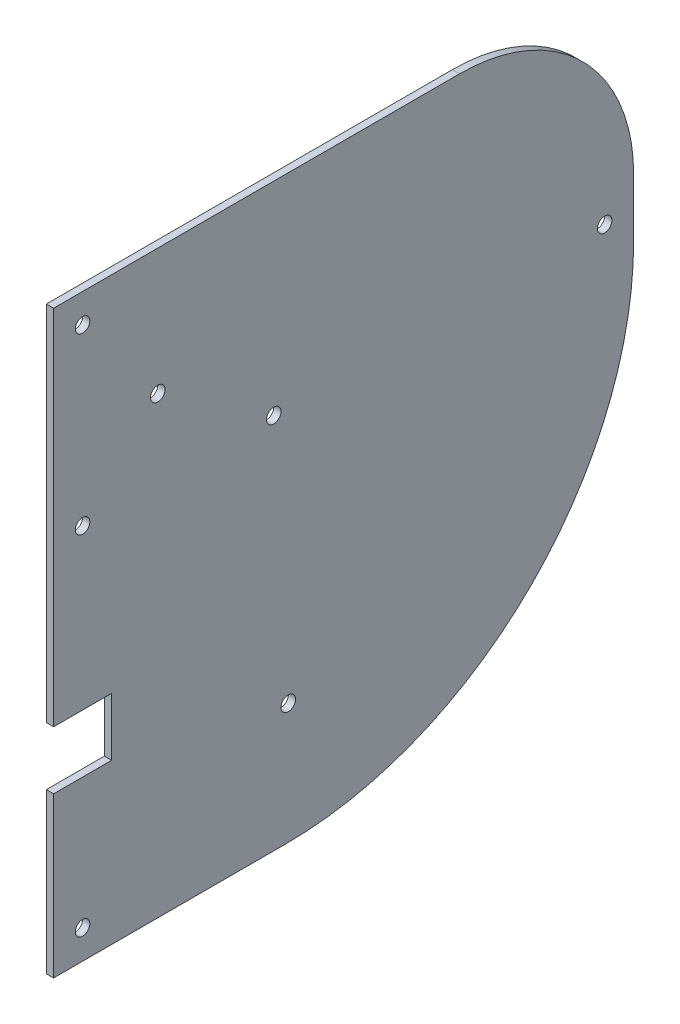
SolidWorks part; units mm, degrees
material "6061-T6 (SS)"
ref_plane "Front Plane" through (0, 0, 0) normal (0, 0, 1) x (1, 0, 0)
ref_plane "Top Plane" through (0, 0, 0) normal (0, 1, 0) x (1, 0, 0)
ref_plane "Right Plane" through (0, 0, 0) normal (1, 0, 0) x (0, 0, -1)
sketch "Sketch1" plane through (0, 0, 0) normal (1, 0, 0) x (0, 0, -1)
  line L1 (0, 0) -> (254, 0)
  line L2 (0, 0) -> (0, 254)
  line L3 (0, 254) -> (254, 254)
  line L4 (254, 0) -> (254, 254)
  line L5 (0, 0) -> (254, 254) construction
  line L6 (0, 254) -> (254, 0) construction
  point P4 (127, 127)
  dimension "D1" = 254
  dimension "D2" = 254
extrude "Boss-Extrude1" add sketch "Sketch1" along normal blind 3.175
sketch "Sketch2" plane through (3.175, 0, 0) normal (1, 0, 0) x (0, 0, -1)
  line L0 (0, 254) -> (0, 0) construction
  line L1 (0, 95.25) -> (25.4, 95.25)
  line L2 (0, 95.25) -> (0, 69.85)
  line L3 (0, 69.85) -> (25.4, 69.85)
  line L4 (25.4, 95.25) -> (25.4, 69.85)
  line L5 (0, 95.25) -> (25.4, 69.85) construction
  line L6 (0, 69.85) -> (25.4, 95.25) construction
  line L7 (0, 0) -> (254, 0) construction
  line L8 (0, 165.1) -> (254, 165.1) construction
  line L9 (254, 0) -> (254, 254) construction
  line L10 (12.7, 254) -> (12.7, 0) construction
  line L11 (254, 254) -> (0, 254) construction
  circle A0 centre (102.775, 52.775) radius 3.175 construction
  circle A1 centre (96.425, 165.1) radius 3.175 construction
  circle A2 centre (45.625, 198.825) radius 3.175 construction
  circle A3 centre (102.775, 52.775) radius 3.175
  circle A4 centre (96.425, 165.1) radius 3.175
  circle A5 centre (45.625, 198.825) radius 3.175
  circle A6 centre (12.7, 165.1) radius 3.175
  circle A7 centre (12.7, 241.3) radius 3.175
  circle A8 centre (12.7, 12.7) radius 3.175
  circle A9 centre (241.3, 165.1) radius 3.175
  point P4 (12.7, 82.55)
  dimension "D4" = 6.35
  dimension "D1" = 25.4
  dimension "D2" = 69.85
  dimension "D3" = 165.1
  dimension "D5" = 12.7
  dimension "D6" = 12.7
  dimension "D7" = 12.7
extrude "Cut-Extrude1" cut sketch "Sketch2" against normal through all
sketch "Sketch3" [suppressed] plane through (0, 0, 0) normal (-1, 0, 0) x (0, 0, 1)
  line L0 (0, 254) -> (0, 0) construction
  line L1 (0, 69.85) -> (-25.4, 69.85)
  line L2 (0, 69.85) -> (0, 95.25)
  line L3 (0, 95.25) -> (-25.4, 95.25)
  line L4 (-25.4, 69.85) -> (-25.4, 95.25)
  line L5 (0, 69.85) -> (-25.4, 95.25) construction
  line L6 (0, 95.25) -> (-25.4, 69.85) construction
  line L7 (-25.4, 95.25) -> (0, 95.25) construction
  line L8 (-25.4, 69.85) -> (-25.4, 95.25) construction
  line L9 (0, 69.85) -> (-25.4, 69.85) construction
  circle A0 centre (-64.675, 103.575) radius 3.175 construction
  circle A1 centre (-128.175, 165.1) radius 3.175 construction
  circle A2 centre (-37.6875, 211.525) radius 3.175 construction
  circle A3 centre (-64.675, 103.575) radius 3.175
  circle A4 centre (-128.175, 165.1) radius 3.175
  circle A5 centre (-37.6875, 211.525) radius 3.175
  circle A6 centre (-12.7, 12.7) radius 3.175 construction
  circle A7 centre (-12.7, 165.1) radius 3.175 construction
  circle A8 centre (-12.7, 241.3) radius 3.175 construction
  circle A9 centre (-241.3, 165.1) radius 3.175 construction
  circle A10 centre (-12.7, 12.7) radius 3.175
  circle A11 centre (-12.7, 165.1) radius 3.175
  circle A12 centre (-12.7, 241.3) radius 3.175
  circle A13 centre (-241.3, 165.1) radius 3.175
  point P4 (-12.7, 82.55)
extrude "Cut-Extrude2" [suppressed] cut sketch "Sketch3" against normal through all
fillet "Fillet1" radius 152.4 1 edges at (1.5875, 0, -254)
fillet "Fillet2" radius 76.2 1 edges at (1.5875, 254, -254)
